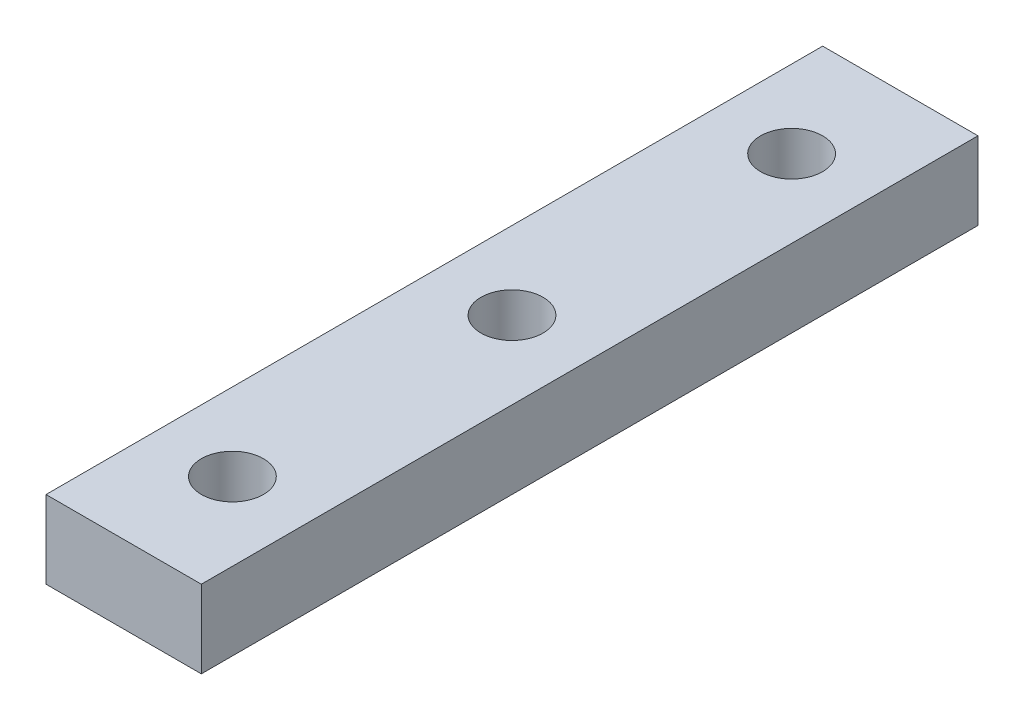
SolidWorks part; units mm, degrees
ref_plane "Front Plane" through (0, 0, 0) normal (0, 0, 1) x (1, 0, 0)
ref_plane "Top Plane" through (0, 0, 0) normal (0, 1, 0) x (1, 0, 0)
ref_plane "Right Plane" through (0, 0, 0) normal (1, 0, 0) x (0, 0, -1)
sketch "Sketch1" plane through (0, 0, 0) normal (0, 0, 1) x (1, 0, 0)
  line L1 (-5, 2.5) -> (5, 2.5)
  line L2 (-5, 2.5) -> (-5, -2.5)
  line L3 (-5, -2.5) -> (5, -2.5)
  line L4 (5, 2.5) -> (5, -2.5)
  dimension "D1" = 10
  dimension "D2" = 5
  dimension "D3" = 5
  dimension "D4" = 2.5
extrude "Boss-Extrude1" add sketch "Sketch1" along normal blind 50
sketch "Sketch2" plane through (0, 2.5, 0) normal (0, 1, 0) x (1, 0, 0)
  line L0 (5, -25) -> (-6.9585, -25) construction
  line L1 (5, -50) -> (5, 0) construction
  line L2 (0, -25) -> (0, -34.9253) construction
  circle A0 centre (0, -43) radius 2
  circle A1 centre (0, -25) radius 2
  circle A2 centre (0, -7) radius 2
  dimension "D1" = 4
  dimension "D2" = 4
  dimension "D3" = 4
  dimension "D4" = 18
  dimension "D5" = 18
extrude "Cut-Extrude1" cut sketch "Sketch2" against normal blind 10
